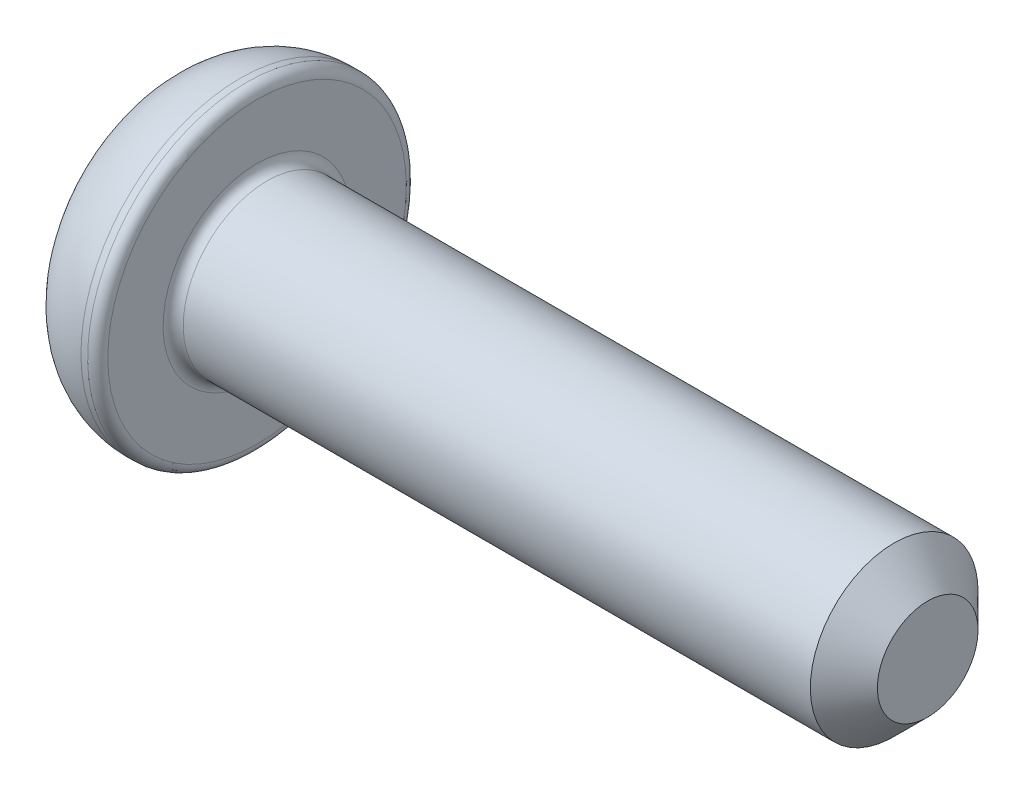
SolidWorks part; units mm, degrees
ref_plane "Спереди" through (0, 0, 0) normal (0, 0, 1) x (1, 0, 0)
ref_plane "Сверху" through (0, 0, 0) normal (0, 1, 0) x (1, 0, 0)
ref_plane "Справа" through (0, 0, 0) normal (1, 0, 0) x (0, 0, -1)
sketch "Эскиз1" plane through (0, 0, 0) normal (0, 0, 1) x (1, 0, 0)
  line L0 (0, 0) -> (0, 3.625)
  line L1 (2.1, 4.75) -> (2.6, 4.75)
  line L2 (2.6, 4.75) -> (2.6, 2.5)
  line L3 (2.6, 2.5) -> (22.6, 2.5)
  line L4 (22.6, 2.5) -> (22.6, 0)
  line L5 (22.6, 0) -> (0, 0) construction
  line L6 (0, 0) -> (22.6, 0)
  arc A0 (0, 3.625) -> (2.1, 4.75) centre (2.1, 2.2275) cw
  point P9 (2.6, 3.625)
  dimension "D1" = 0.5
  dimension "D2" = 5
  dimension "D3" = 9.5
  dimension "D5" = 2.6
  dimension "D6" = 20
revolve "Повернуть1" add sketch "Эскиз1" angle 360 about L5
cosmetic thread "Условное изображение резьбы1" parameters "D2"=4.11
sketch "Эскиз2" plane through (0, 0, 0) normal (-1, 0, 0) x (0, 0, 1)
  line L1 (0.866, 1.5) -> (-0.866, 1.5)
  line L2 (-0.866, 1.5) -> (-1.7321, 0)
  line L3 (-1.7321, 0) -> (-0.866, -1.5)
  line L4 (-0.866, -1.5) -> (0.866, -1.5)
  line L5 (0.866, -1.5) -> (1.7321, 0)
  line L6 (1.7321, 0) -> (0.866, 1.5)
  circle A0 centre (0, 0) radius 1.5 construction
  dimension "D1" = 3
extrude "Вырез-Вытянуть1" cut sketch "Эскиз2" against normal blind 1.5
fillet "Скругление1" radius 0.3 2 edges at (2.6, 2.5, 0) (2.6, 4.75, 0)
chamfer "Фаска1" distance 1 angle 45 1 edges at (22.6, 2.5, 0)
